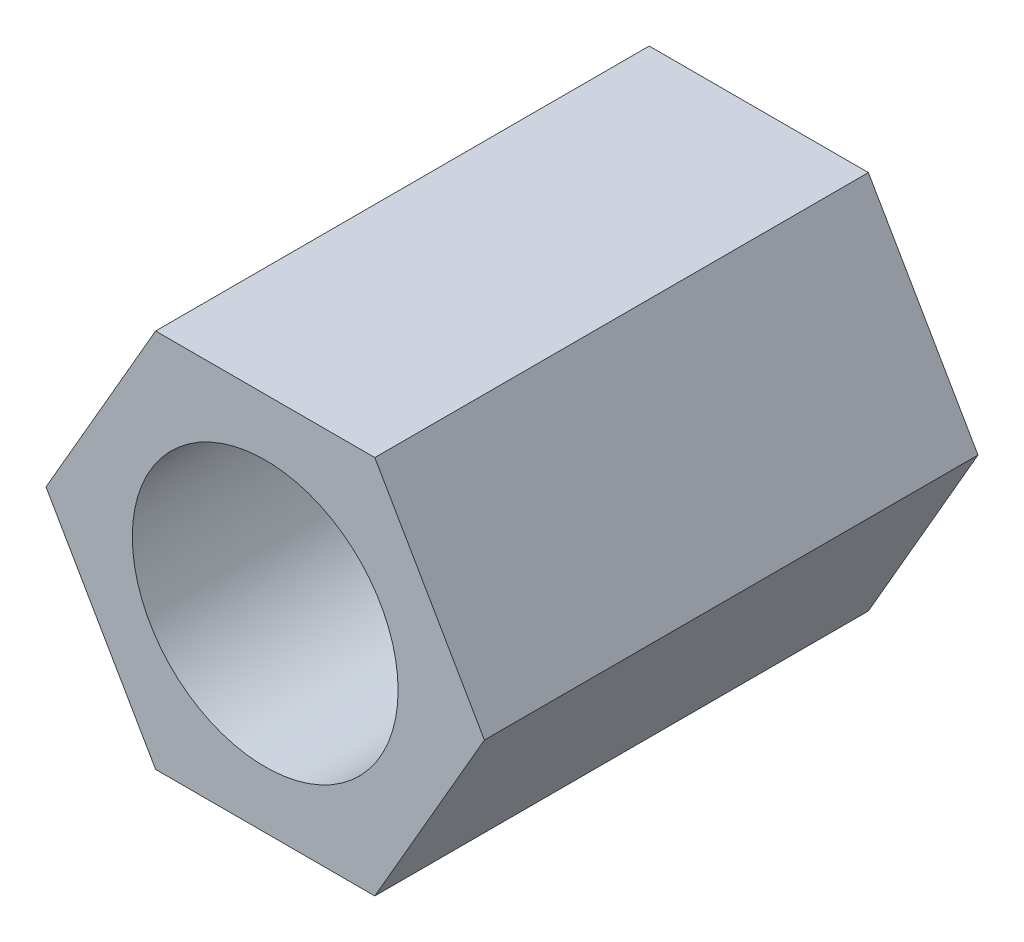
SolidWorks part; units mm, degrees
material "1.0301 (C10)"
ref_plane "Piano frontale" through (0, 0, 0) normal (0, 0, 1) x (1, 0, 0)
ref_plane "Piano superiore" through (0, 0, 0) normal (0, 1, 0) x (1, 0, 0)
ref_plane "Piano destro" through (0, 0, 0) normal (1, 0, 0) x (0, 0, -1)
sketch "Schizzo1" plane through (0, 0, 0) normal (0, 0, 1) x (1, 0, 0)
  line L1 (1.4434, 2.5) -> (-1.4434, 2.5)
  line L2 (-1.4434, 2.5) -> (-2.8868, 0)
  line L3 (-2.8868, 0) -> (-1.4434, -2.5)
  line L4 (-1.4434, -2.5) -> (1.4434, -2.5)
  line L5 (1.4434, -2.5) -> (2.8868, 0)
  line L6 (2.8868, 0) -> (1.4434, 2.5)
  circle A0 centre (0, 0) radius 2.5 construction
  dimension "D1" = 5
extrude "Estrusione-Estrusione1" add sketch "Schizzo1" along normal blind 6.5
sketch "Schizzo2" plane through (0, 0, 6.5) normal (0, 0, 1) x (1, 0, 0)
  circle A0 centre (0, 0) radius 1.75
  dimension "D1" = 3.5
extrude "Taglio-Estrusione1" cut sketch "Schizzo2" against normal blind 15
